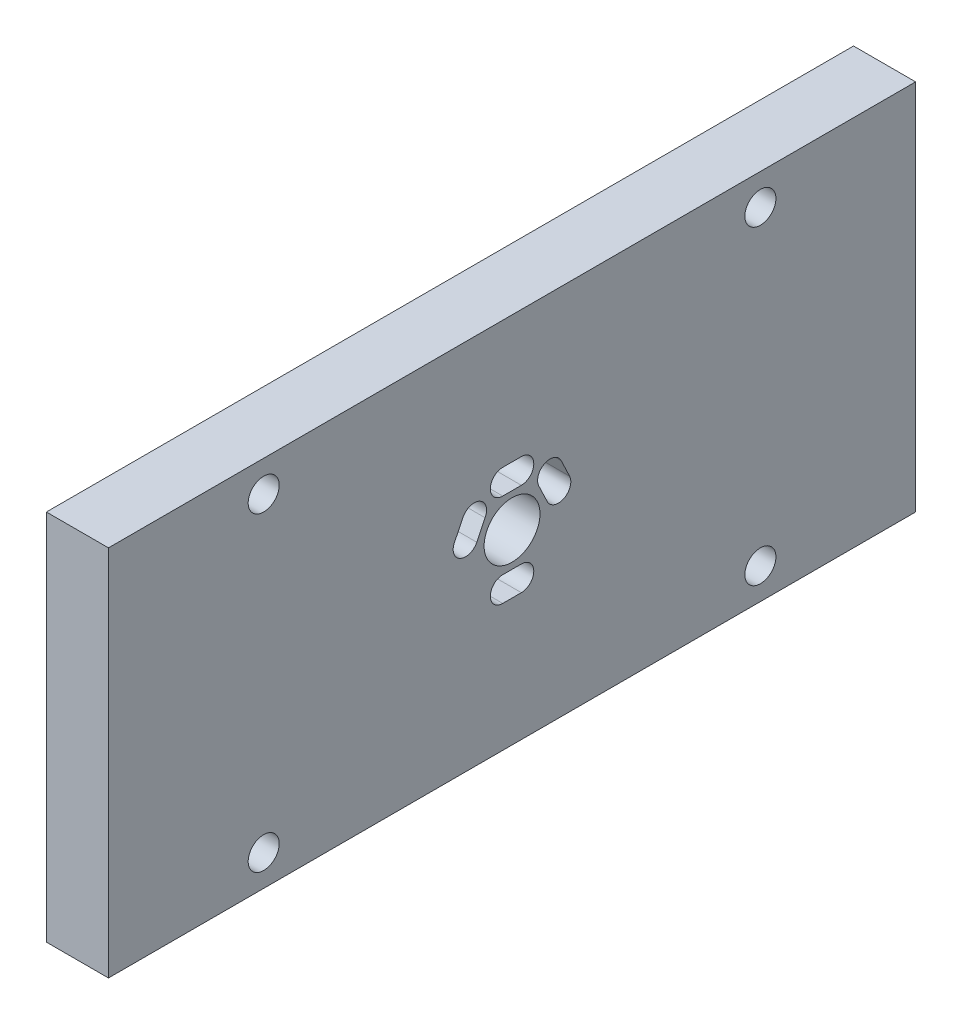
SolidWorks part; units mm, degrees
ref_plane "Front Plane" through (0, 0, 0) normal (0, 0, 1) x (1, 0, 0)
ref_plane "Top Plane" through (0, 0, 0) normal (0, 1, 0) x (1, 0, 0)
ref_plane "Right Plane" through (0, 0, 0) normal (1, 0, 0) x (0, 0, -1)
sketch "Sketch1" plane through (0, 0, 0) normal (1, 0, 0) x (0, 0, -1)
  line L9 (-61.1868, 57.8975) -> (68.8132, 57.8975)
  line L10 (-61.1868, 57.8975) -> (-61.1868, -2.1025)
  line L11 (-61.1868, -2.1025) -> (68.8132, -2.1025)
  line L12 (68.8132, 57.8975) -> (68.8132, -2.1025)
  circle A0 centre (-36.1868, 52.8975) radius 2.5
  circle A1 centre (-36.1868, 2.8975) radius 2.5
  circle A2 centre (43.8132, 2.8975) radius 2.5
  circle A3 centre (43.8132, 52.8975) radius 2.5
  line B0 (-5.4644, 30.7753) -> (-4.0816, 33.6063)
  line B1 (5.3132, 18.3975) -> (2.3132, 18.3975)
  line B2 (-0.5284, 31.7706) -> (-1.8696, 29.0208)
  line B3 (2.3132, 22.3975) -> (5.3132, 22.3975)
  line B4 (5.3132, 33.3742) -> (2.3132, 33.3742)
  line B5 (9.472, 29.0382) -> (8.081, 31.9616)
  line B6 (2.3132, 37.3742) -> (5.3132, 37.3742)
  line B7 (11.7336, 33.5893) -> (13.0834, 30.7583)
  circle B8 centre (3.8132, 27.8975) radius 4.5
  arc B9 (9.472, 29.0382) -> (13.0834, 30.7583) centre (11.2777, 29.8983) ccw
  arc B10 (11.7336, 33.5893) -> (8.081, 31.9616) centre (9.9281, 32.729) ccw
  arc B11 (-5.4644, 30.7753) -> (-1.8696, 29.0208) centre (-3.6672, 29.8975) ccw
  arc B12 (-0.5284, 31.7706) -> (-4.0816, 33.6063) centre (-2.2872, 32.7228) ccw
  arc B13 (2.3132, 37.3742) -> (2.3132, 33.3742) centre (2.3132, 35.3742) ccw
  arc B14 (5.3132, 33.3742) -> (5.3132, 37.3742) centre (5.3132, 35.3742) ccw
  arc B15 (2.3132, 22.3975) -> (2.3132, 18.3975) centre (2.3132, 20.3975) ccw
  arc B16 (5.3132, 18.3975) -> (5.3132, 22.3975) centre (5.3132, 20.3975) ccw
  dimension "D5" = 5
  dimension "D8" = 5
  dimension "D11" = 5
  dimension "D14" = 5
  dimension "D1" = 130
  dimension "D2" = 60
  dimension "D3" = 30
  dimension "D4" = 65
  dimension "D6" = 5
  dimension "D7" = 25
  dimension "D9" = 25
  dimension "D10" = 5
  dimension "D12" = 25
  dimension "D13" = 5
  dimension "D15" = 5
  dimension "D16" = 25
sketch_block_instance "Block1-1"
sketch_block "Block1"
extrude "Boss-Extrude1" add sketch "Sketch1" along normal blind 10
